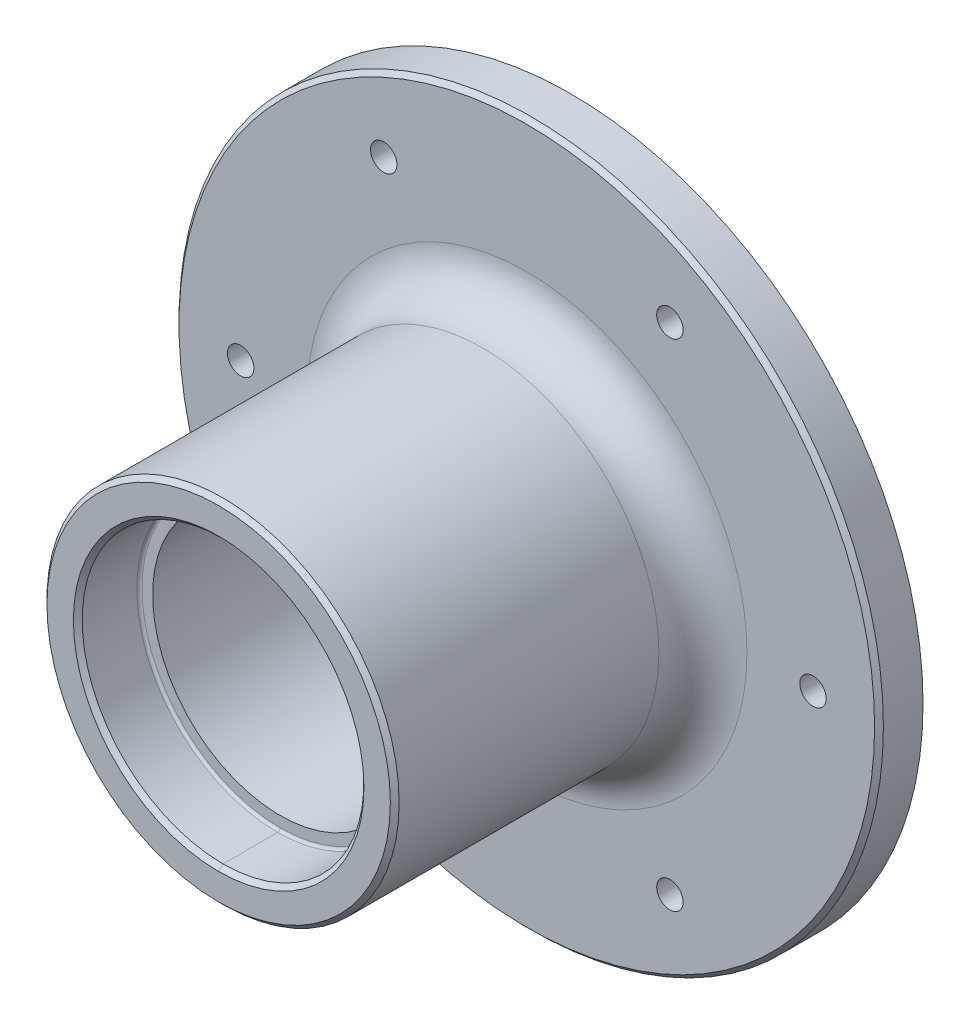
SolidWorks part; units mm, degrees
material "6063-T6"
ref_plane "Front Plane" through (0, 0, 0) normal (0, 0, 1) x (1, 0, 0)
ref_plane "Top Plane" through (0, 0, 0) normal (0, 1, 0) x (1, 0, 0)
ref_plane "Right Plane" through (0, 0, 0) normal (1, 0, 0) x (0, 0, -1)
sketch "Sketch1" plane through (0, 0, 0) normal (0, 0, 1) x (1, 0, 0)
  circle A0 centre (0, 0) radius 40
  dimension "D2" = 80
extrude "Boss-Extrude1" add sketch "Sketch1" along normal blind 5
sketch "Sketch2" plane through (0, 0, 5) normal (0, 0, 1) x (1, 0, 0)
  circle A0 centre (0, 0) radius 20
  dimension "D2" = 40
extrude "Boss-Extrude2" add sketch "Sketch2" along normal blind 35
ref_axis "Axis1" through (0, 0, 56.3012) along (0, 0, -1)
sketch "Sketch6" plane through (0, 0, 0) normal (1, 0, 0) x (0, 0, -1)
  line L0 (0, 0) -> (-40, 0)
  line L1 (-40, 20) -> (-40, -20) construction
  line L2 (-40, 0) -> (-40, 16)
  line L3 (-40, 20) -> (-40, -20) construction
  line L4 (-40, 16) -> (-33, 16)
  line L5 (-33, 16) -> (-33, 14.5)
  line L6 (-33, 14.5) -> (-7, 14.5)
  line L8 (-7, 16) -> (0, 16)
  line L9 (0, -40) -> (0, 40) construction
  line L10 (0, 16) -> (0, 0)
  line L11 (-7, 14.5) -> (-7, 16)
  dimension "D1" = 14.5
  dimension "D2" = 7
  dimension "D3" = 16
  dimension "D5" = 7
revolve "Cut-Revolve2" cut sketch "Sketch6" angle 360 about axis through (0, 0, 56.3012) along (0, 0, -1)
hole_wizard "M4 Tapped Hole1" positions "Sketch9" profile "Sketch8" tap size "M4" standard "ISO" end condition through all
sketch "Sketch9" plane through (0, 0, 0) normal (0, 0, 1) x (1, 0, 0)
  circle A0 centre (0, 0) radius 32.5 construction
  point P0 (32.5, 0)
  dimension "D1" = 65
sketch "Sketch8" plane through (32.5, 0, 0) normal (1, 0, 0) x (0, 1, 0)
  line L0 (0, 0) -> (0, 40)
  line L1 (0, 40) -> (1.5, 40)
  line L2 (1.5, 40) -> (1.5, 0)
  line L5 (1.5, 0) -> (0, 0)
  line L11 (0, -6.35) -> (0, 107.95) construction
  dimension "Thru Tap Drill Dia." = 3
  dimension "Thru Tap Drill Depth" = 40
cosmetic thread "Hole Thread2" parameters "D2"=4
pattern_circular "CirPattern2" count 6 over 360 about axis through (0, 0, 0) along (0, 0, 1) of "M4 Tapped Hole1"
sketch "Sketch10" plane through (0, 0, 0) normal (0, 1, 0) x (0, 0, -1)
  line L0 (-7, 0) -> (0, 0)
  line L2 (-40, 0) -> (-33, 0)
  line L4 (-33, 16) -> (-33, -16) construction
split line "Split Line1"
ref_plane "Plane1" through (0, 0, 3.5) normal (0, 0, -1) x (-1, 0, 0)
ref_point "Point1"
ref_plane "Plane2" through (0, 0, 36.5) normal (0, 0, 1) x (1, 0, 0)
ref_point "Point2"
chamfer "Chamfer2" distance 0.5 angle 45 6 edges at (40, 0, 5) (20, 0, 40) (-16, 0, 40) (16, 0, 40) (-16, 0, 0) (16, 0, 0)
fillet "Fillet1" radius 5 1 edges at (20, 0, 5)
fillet "Fillet2" radius 0.3 4 edges at (-16, 0, 33) (16, 0, 33) (-16, 0, 7) (16, 0, 7)
